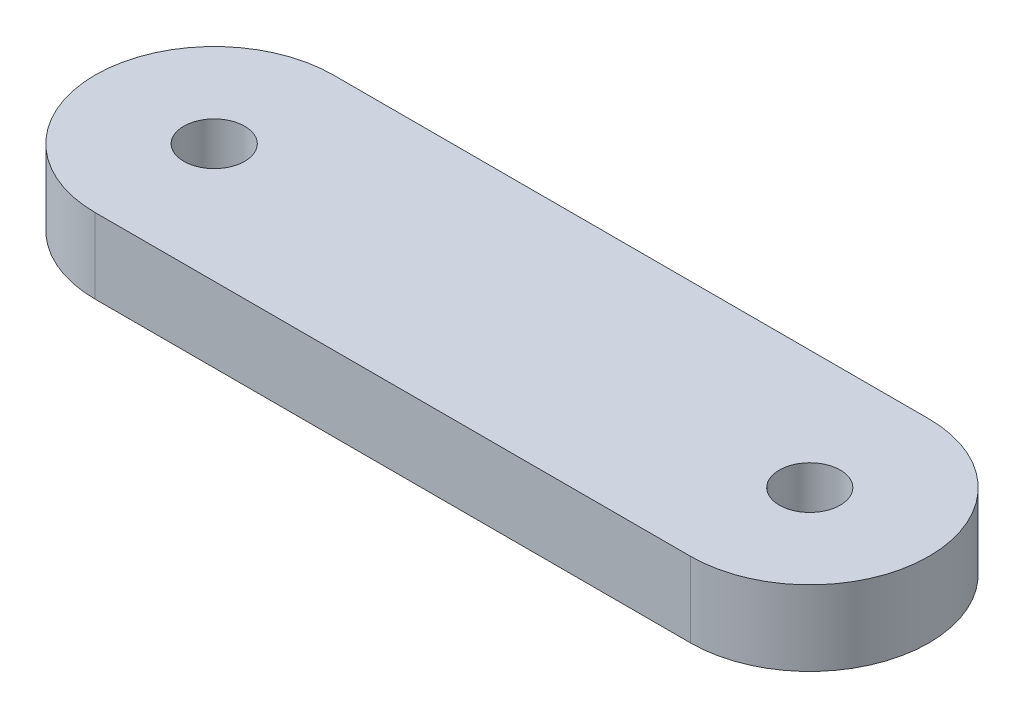
SolidWorks part; units mm, degrees
ref_plane "Front Plane" through (0, 0, 0) normal (0, 0, 1) x (1, 0, 0)
ref_plane "Top Plane" through (0, 0, 0) normal (0, 1, 0) x (1, 0, 0)
ref_plane "Right Plane" through (0, 0, 0) normal (1, 0, 0) x (0, 0, -1)
sketch "Sketch1" plane through (0, 0, 0) normal (0, 1, 0) x (1, 0, 0)
  line L1 (-18.6184, -6.35) -> (13.1316, -6.35)
  line L3 (-18.6184, 6.35) -> (13.1316, 6.35)
  arc A0 (13.1316, -6.35) -> (13.1316, 6.35) centre (13.1316, 0) ccw
  arc A1 (-18.6184, 6.35) -> (-18.6184, -6.35) centre (-18.6184, 0) ccw
  circle A2 centre (-18.6184, 0) radius 1.625
  circle A3 centre (13.1316, 0) radius 1.625
  point P0 (0, 0)
  dimension "D3" = 3.25
  dimension "D4" = 3.25
  dimension "D1" = 12.7
  dimension "D2" = 31.75
extrude "Boss-Extrude1" add sketch "Sketch1" along normal blind 4
